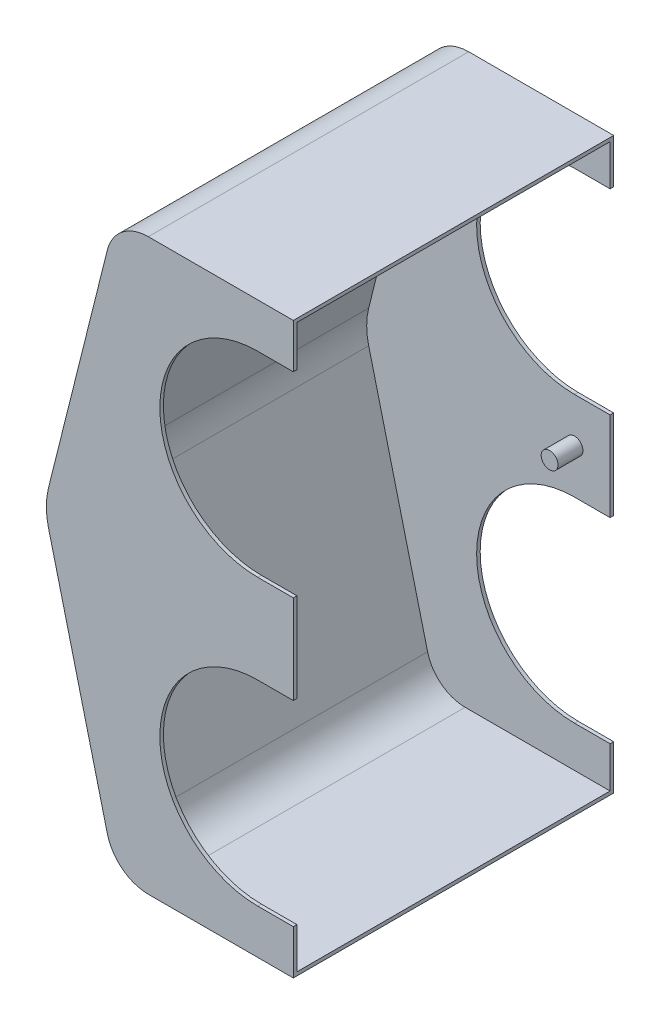
SolidWorks part; units mm, degrees
material "ABS PC"
ref_plane "Front Plane" through (0, 0, 0) normal (0, 0, 1) x (1, 0, 0)
ref_plane "Top Plane" through (0, 0, 0) normal (0, 1, 0) x (1, 0, 0)
ref_plane "Right Plane" through (0, 0, 0) normal (1, 0, 0) x (0, 0, -1)
sketch "Sketch1" plane through (0, 0, 0) normal (1, 0, 0) x (0, 0, -1)
  line L1 (0, 0) -> (114.3, 0)
  line L2 (0, 0) -> (0, -203.2)
  line L3 (0, -203.2) -> (114.3, -203.2)
  line L4 (114.3, 0) -> (114.3, -203.2)
  point P4 (-54.5201, 88.1278)
  point P5 (0, 0)
  point P6 (0, 0)
  dimension "D1" = 203.2
  dimension "D2" = 114.3
extrude "Boss-Extrude1" add sketch "Sketch1" against normal blind 88.9
sketch "Sketch4" plane through (0, 0, -114.3) normal (0, 0, -1) x (-1, 0, 0)
  line L0 (63.5, 0) -> (88.9, -101.6)
  line L1 (88.9, -101.6) -> (63.5, -203.2)
  line L2 (48.895, 0) -> (-48.895, 0) construction
  line L3 (88.9, -203.2) -> (0, -203.2) construction
  line L4 (88.9, -203.2) -> (88.9, 0) construction
  line L9 (63.5, 0) -> (88.9, 0)
  line L10 (88.9, 0) -> (88.9, -203.2)
  line L11 (88.9, -203.2) -> (63.5, -203.2)
  point P2 (0, 0)
  point P10 (63.8114, -201.9545)
  point P13 (88.9, -101.6)
  point P14 (0, 0)
  point P15 (0, 0)
  point P19 (0, 0)
  point P20 (88.9, 0)
  point P21 (85.4907, 0)
  line M6 (0, -203.2) -> (88.9, -203.2)
  line M7 (88.9, -203.2) -> (88.9, 0)
  line M8 (88.9, 0) -> (0, 0)
  dimension "D1" = 25.4
  dimension "D2" = 25.4
extrude "Cut-Extrude1" cut sketch "Sketch4" against normal through all contours L0 M8 M7 | L1 M7 M6
fillet "Fillet1" radius 25.24 1 edges at (-88.9, -101.6, -57.15)
fillet "Fillet2" radius 15.08 2 edges at (-63.5, 0, -57.15) (-63.5, -203.2, -57.15)
sketch "Sketch5" plane through (0, 0, 0) normal (0, 0, 1) x (1, 0, 0)
  line L0 (-60.5871, -101.6) -> (-23.5513, -101.6) construction
  line L1 (0, 0) -> (0, -203.2) construction
  line L2 (-12.7, -187.325) -> (0, -187.325)
  line L3 (-12.7, -117.475) -> (0, -117.475)
  line L4 (0, -187.325) -> (0, -117.475)
  arc A0 (-12.7, -117.475) -> (-12.7, -187.325) centre (-12.7, -152.4) ccw
  point P4 (0, -101.6)
  dimension "D3" = 69.85
  dimension "D1" = 50.8
  dimension "D2" = 12.7
extrude "Cut-Extrude2" cut sketch "Sketch5" against normal through all
pattern_linear "LPattern1" count 2 spacing 101.6 along (0, 1, 0) of "Cut-Extrude2"
shell "Shell5" thickness 1.27
sketch "Sketch9" plane through (0, 0, -113.03) normal (0, 0, 1) x (1, 0, 0)
  line L0 (0, -117.475) -> (0, -85.725) construction
  circle A0 centre (-12.7, -101.6) radius 3
  point P4 (0, -101.6)
  point P5 (-12.1307, -111.1178)
  point P6 (0, 0)
  dimension "D1" = 12.7
extrude "Boss-Extrude2" add sketch "Sketch9" along normal blind 8.89
ref_plane "Plane1" through (0, 0, -57.15) normal (0, 0, 1) x (1, 0, 0)
mirror "Mirror1" about plane through (0, 0, -57.15) normal (0, 0, 1) of "Boss-Extrude2"
